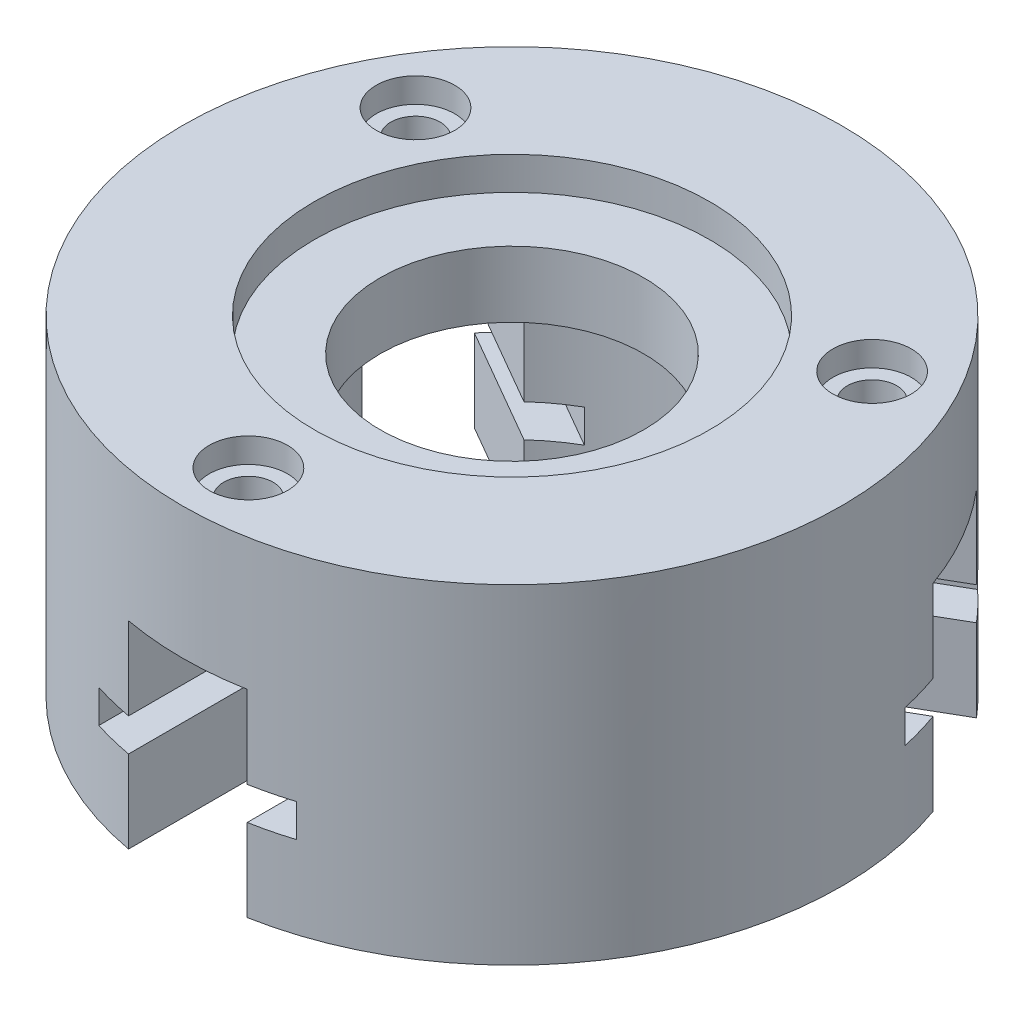
SolidWorks part; units mm, degrees
material "AISI 304"
ref_plane "Front Plane" through (0, 0, 0) normal (0, 0, 1) x (1, 0, 0)
ref_plane "Top Plane" through (0, 0, 0) normal (0, 1, 0) x (1, 0, 0)
ref_plane "Right Plane" through (0, 0, 0) normal (1, 0, 0) x (0, 0, -1)
sketch "Sketch6" plane through (0, 0, 0) normal (0, 1, 0) x (0, 0, -1)
  circle A0 centre (0, 0) radius 100
  circle A1 centre (0, 0) radius 40
  dimension "D1" = 200
  dimension "D2" = 80
extrude "Boss-Extrude2" add sketch "Sketch6" along normal mid plane 100
sketch "Sketch7" plane through (0, 50, 0) normal (0, 1, 0) x (0, 0, -1)
  circle A0 centre (0, 0) radius 60
  dimension "D1" = 120
extrude "Cut-Extrude4" cut sketch "Sketch7" against normal blind 10
sketch "Sketch8" plane through (0, -50, 0) normal (0, -1, 0) x (0, 0, 1)
  circle A0 centre (0, 0) radius 60
  dimension "D1" = 120
extrude "Cut-Extrude5" cut sketch "Sketch8" against normal blind 70
sketch "Sketch9" plane through (0, 0, 0) normal (0, 0, 1) x (0, -1, 0)
  line L0 (-104.6317, 0) -> (104.6317, 0) construction
  line L1 (50, -18) -> (50, 18)
  line L2 (50, -100) -> (50, 100) construction
  line L3 (50, 18) -> (25, 18)
  line L4 (15, 18) -> (15, 30)
  line L5 (15, 30) -> (25, 30)
  line L6 (25, 30) -> (25, 18)
  line L7 (15, 18) -> (-10, 18)
  line L8 (-10, 18) -> (-10, -18)
  line L9 (15, -18) -> (-10, -18)
  line L10 (25, -30) -> (25, -18)
  line L11 (15, -30) -> (25, -30)
  line L12 (15, -18) -> (15, -30)
  line L13 (50, -18) -> (25, -18)
  point P4 (0, 0)
  point P18 (-10, 0)
  point P23 (50, 0)
  dimension "D1" = 36
  dimension "D2" = 60
  dimension "D3" = 10
  dimension "D4" = 60
  dimension "D5" = 25
extrude "Cut-Extrude6" cut sketch "Sketch9" along normal through all
hole_wizard "CBORE for M12 Hex Head Bolt1" positions "Sketch10" profile "Sketch11" counterbore size "M12" standard "ISO" end condition through all
sketch "Sketch10" plane through (0, 50, 0) normal (0, 1, 0) x (1, 0, 0)
  point P0 (0, -80)
  dimension "D1" = 80
sketch "Sketch11" plane through (0, 50, 80) normal (1, 0, 0) x (0, 0, 1)
  line L0 (0, 0) -> (0, 100)
  line L1 (0, 100) -> (7.5, 100)
  line L3 (7.5, 100) -> (7.5, 7.5)
  line L4 (7.5, 7.5) -> (11.8925, 7.5)
  line L5 (11.8925, 7.5) -> (11.8925, 0)
  line L7 (11.8925, 0) -> (0, 0)
  line L11 (0, -6.35) -> (0, 107.95) construction
  dimension "Thru Hole Dia." = 15
  dimension "Thru Hole Depth" = 100
  dimension "C'Bore Dia." = 23.785
  dimension "C'Bore Depth" = 7.5
pattern_circular "CirPattern2" count 3 over 360 about axis through (0, 0, 0) along (0, 1, 0) of "Cut-Extrude6", "CBORE for M12 Hex Head Bolt1"
